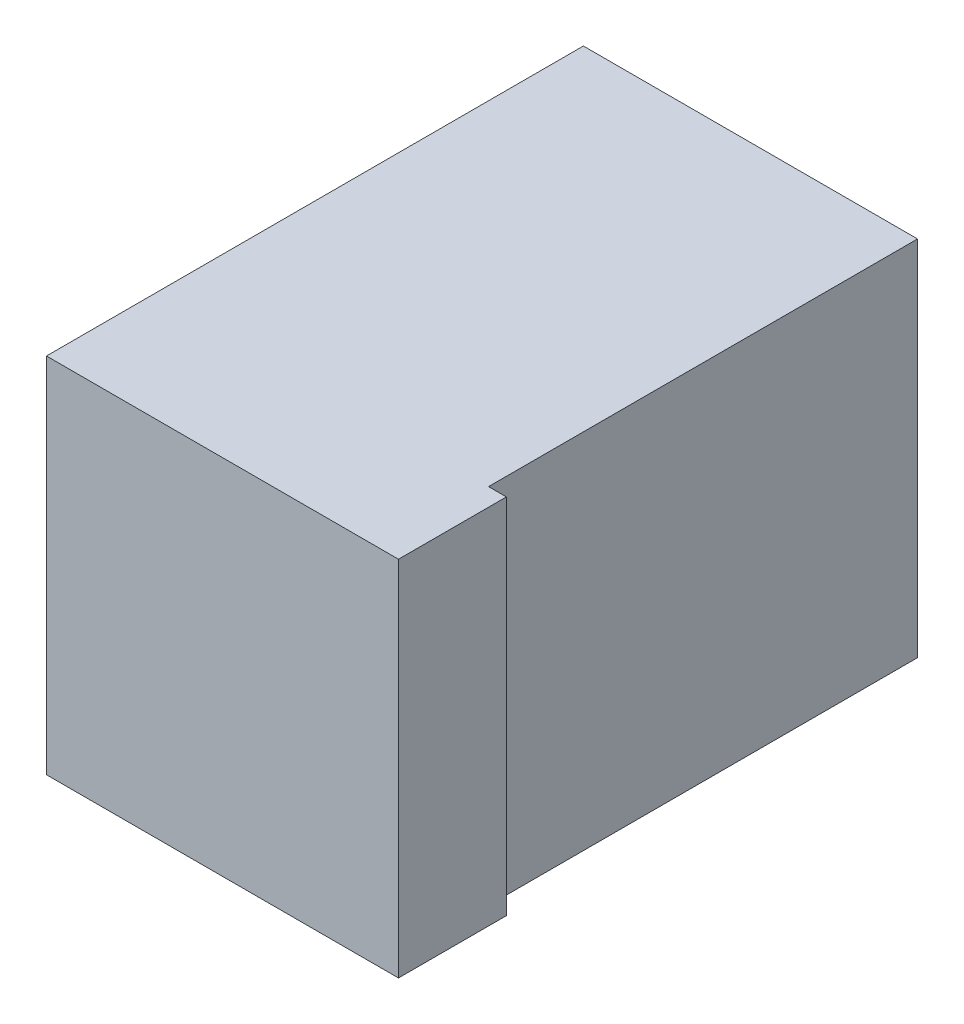
SolidWorks part; units mm, degrees
material "Copper"
ref_plane "Front Plane" through (0, 0, 0) normal (0, 0, 1) x (1, 0, 0)
ref_plane "Top Plane" through (0, 0, 0) normal (0, 1, 0) x (1, 0, 0)
ref_plane "Right Plane" through (0, 0, 0) normal (1, 0, 0) x (0, 0, -1)
sketch "Sketch1" plane through (0, 0, 0) normal (0, 0, 1) x (1, 0, 0)
  line L1 (0, 0) -> (-99, 0)
  line L2 (0, 0) -> (0, -102)
  line L3 (0, -102) -> (-99, -102)
  line L4 (-99, 0) -> (-99, -102)
  dimension "D1" = 99
  dimension "D2" = 102
extrude "Boss-Extrude1" add sketch "Sketch1" along normal blind 151
sketch "Sketch3" plane through (0, -102, 0) normal (0, -1, 0) x (1, 0, 0)
  line L0 (-99, 151) -> (-99, 0) construction
  line L1 (0, 0) -> (-5.02, 0)
  line L2 (0, 0) -> (0, 120.65)
  line L3 (0, 120.65) -> (-5.02, 120.65)
  line L4 (-5.02, 0) -> (-5.02, 120.65)
  dimension "D1" = 120.65
  dimension "D2" = 93.98
extrude "Cut-Extrude2" cut sketch "Sketch3" against normal blind 152.4
ref_plane "Midplane 1" through (0, -51, 0) normal (0, -1, 0) x (-1, 0, 0)
ref_plane "Midplane 2" through (0, 0, 75.5) normal (0, 0, 1) x (1, 0, 0)
